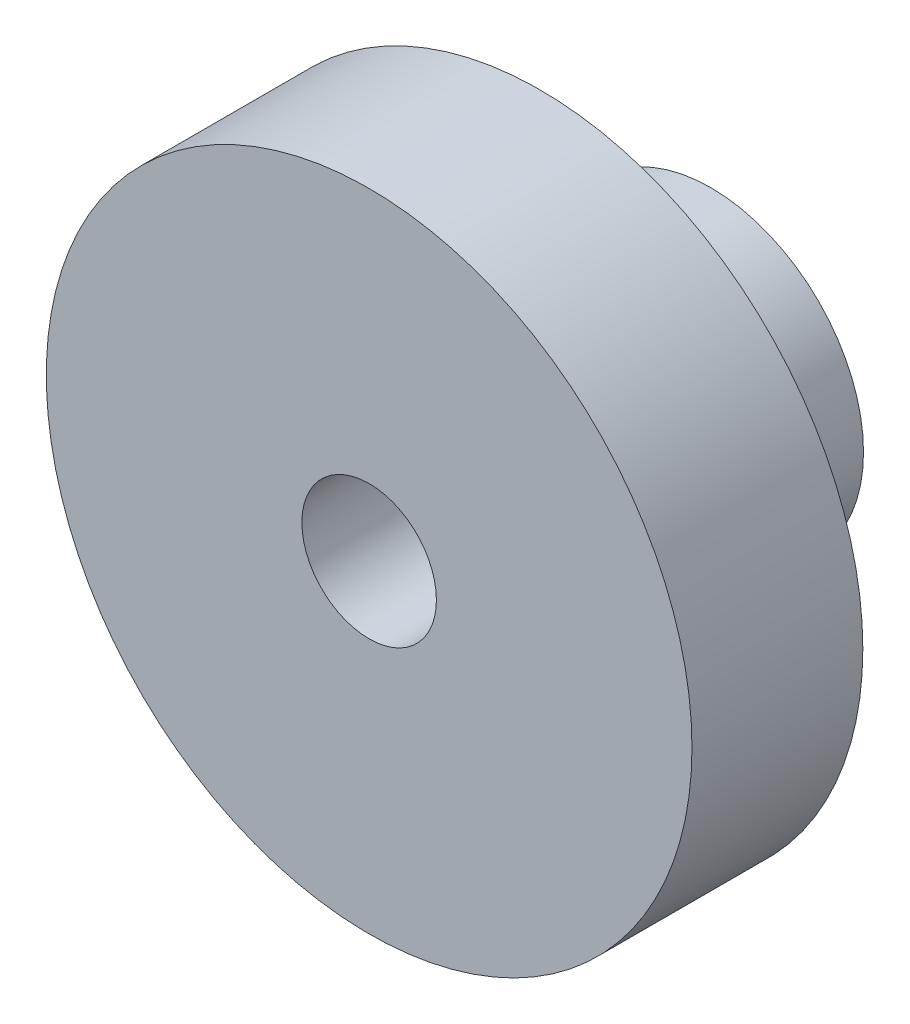
SolidWorks part; units mm, degrees
ref_plane "Front Plane" through (0, 0, 0) normal (0, 0, 1) x (1, 0, 0)
ref_plane "Top Plane" through (0, 0, 0) normal (0, 1, 0) x (1, 0, 0)
ref_plane "Right Plane" through (0, 0, 0) normal (1, 0, 0) x (0, 0, -1)
sketch "Sketch1" plane through (0, 0, 0) normal (0, 0, 1) x (1, 0, 0)
  circle A0 centre (0, 0) radius 12
  circle A1 centre (0, 0) radius 2.5
  dimension "D1" = 24
  dimension "D2" = 5
extrude "Boss-Extrude1" add sketch "Sketch1" along normal blind 6.35
sketch "Sketch2" plane through (0, 0, 0) normal (0, 0, -1) x (-1, 0, 0)
  circle A0 centre (0, 0) radius 2.5
  circle A1 centre (0, 0) radius 5.675
  circle A2 centre (0, 0) radius 12 construction
  dimension "D1" = 3.175
  dimension "D2" = 5
extrude "Boss-Extrude2" add sketch "Sketch2" along normal blind 6.35
sketch "Sketch3" plane through (0, 0, -6.35) normal (0, 0, -1) x (-1, 0, 0)
  circle A0 centre (0, 0) radius 1.5875
  circle A1 centre (0, 0) radius 5.675
  circle A2 centre (0, 0) radius 5.675 construction
  dimension "D1" = 3.175
  dimension "D2" = 11.35
extrude "Boss-Extrude3" add sketch "Sketch3" against normal blind 1.5875
